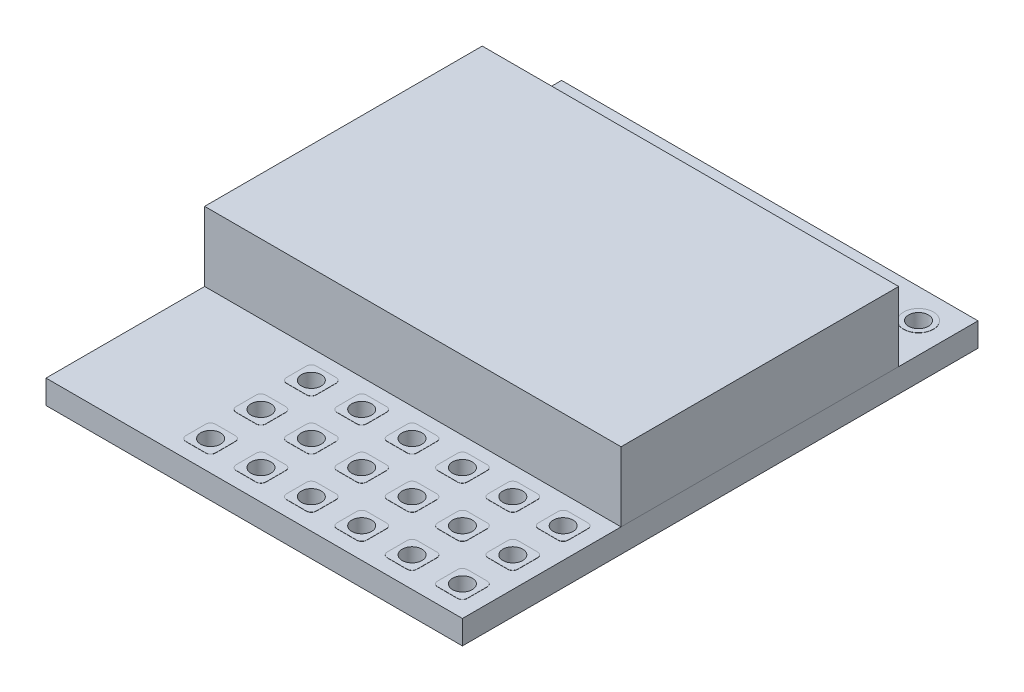
SolidWorks part; units mm, degrees
ref_plane "Front Plane" through (0, 0, 0) normal (0, 0, 1) x (1, 0, 0)
ref_plane "Top Plane" through (0, 0, 0) normal (0, 1, 0) x (1, 0, 0)
ref_plane "Right Plane" through (0, 0, 0) normal (1, 0, 0) x (0, 0, -1)
sketch "Sketch1" plane through (0, 0, 0) normal (0, 1, 0) x (1, 0, 0)
  line L1 (0, 0) -> (21, 0)
  line L2 (0, 0) -> (0, 26)
  line L3 (0, 26) -> (21, 26)
  line L4 (21, 0) -> (21, 26)
  dimension "D1" = 21
  dimension "D2" = 26
extrude "Boss-Extrude1" add sketch "Sketch1" along normal blind 1.2
sketch "Sketch3" plane through (0, 1.2, 0) normal (0, 1, 0) x (1, 0, 0)
  line L0 (21, 0) -> (21, 26) construction
  line L1 (21, 22) -> (0, 22)
  line L2 (21, 22) -> (21, 8)
  line L3 (21, 8) -> (0, 8)
  line L4 (0, 22) -> (0, 8)
  line L5 (0, 26) -> (0, 0) construction
  line L6 (21, 26) -> (0, 26) construction
  dimension "D1" = 14
  dimension "D2" = 4
extrude "Boss-Extrude2" add sketch "Sketch3" along normal blind 3.5 separate body
sketch "Sketch4" plane through (0, 1.2, 0) normal (0, 1, 0) x (1, 0, 0)
  line L0 (21, 0) -> (21, 26) construction
  line L1 (19, 2.25) -> (20, 2.25)
  line L2 (18.75, 2) -> (18.75, 1)
  line L3 (19, 0.75) -> (20, 0.75)
  line L4 (20.25, 2) -> (20.25, 1)
  line L5 (0, 0) -> (21, 0) construction
  line L6 (16.46, 2.25) -> (17.46, 2.25)
  line L7 (16.21, 2) -> (16.21, 1)
  line L8 (16.46, 0.75) -> (17.46, 0.75)
  line L9 (17.71, 2) -> (17.71, 1)
  line L10 (13.92, 2.25) -> (14.92, 2.25)
  line L11 (13.67, 2) -> (13.67, 1)
  line L12 (13.92, 0.75) -> (14.92, 0.75)
  line L13 (15.17, 2) -> (15.17, 1)
  line L14 (11.38, 2.25) -> (12.38, 2.25)
  line L15 (11.13, 2) -> (11.13, 1)
  line L16 (11.38, 0.75) -> (12.38, 0.75)
  line L17 (12.63, 2) -> (12.63, 1)
  line L18 (8.84, 2.25) -> (9.84, 2.25)
  line L19 (8.59, 2) -> (8.59, 1)
  line L20 (8.84, 0.75) -> (9.84, 0.75)
  line L21 (10.09, 2) -> (10.09, 1)
  line L22 (6.3, 2.25) -> (7.3, 2.25)
  line L23 (6.05, 2) -> (6.05, 1)
  line L24 (6.3, 0.75) -> (7.3, 0.75)
  line L25 (7.55, 2) -> (7.55, 1)
  line L26 (16.46, 4.79) -> (17.46, 4.79)
  line L27 (16.21, 4.54) -> (16.21, 3.54)
  line L28 (16.46, 3.29) -> (17.46, 3.29)
  line L29 (17.71, 4.54) -> (17.71, 3.54)
  line L30 (13.92, 4.79) -> (14.92, 4.79)
  line L31 (13.67, 4.54) -> (13.67, 3.54)
  line L32 (13.92, 3.29) -> (14.92, 3.29)
  line L33 (15.17, 4.54) -> (15.17, 3.54)
  line L34 (11.38, 4.79) -> (12.38, 4.79)
  line L35 (11.13, 4.54) -> (11.13, 3.54)
  line L36 (11.38, 3.29) -> (12.38, 3.29)
  line L37 (12.63, 4.54) -> (12.63, 3.54)
  line L38 (8.84, 4.79) -> (9.84, 4.79)
  line L39 (8.59, 4.54) -> (8.59, 3.54)
  line L40 (8.84, 3.29) -> (9.84, 3.29)
  line L41 (10.09, 4.54) -> (10.09, 3.54)
  line L42 (6.3, 4.79) -> (7.3, 4.79)
  line L43 (6.05, 4.54) -> (6.05, 3.54)
  line L44 (6.3, 3.29) -> (7.3, 3.29)
  line L45 (7.55, 4.54) -> (7.55, 3.54)
  line L46 (16.46, 7.33) -> (17.46, 7.33)
  line L47 (16.21, 7.08) -> (16.21, 6.08)
  line L48 (16.46, 5.83) -> (17.46, 5.83)
  line L49 (17.71, 7.08) -> (17.71, 6.08)
  line L50 (13.92, 7.33) -> (14.92, 7.33)
  line L51 (13.67, 7.08) -> (13.67, 6.08)
  line L52 (13.92, 5.83) -> (14.92, 5.83)
  line L53 (15.17, 7.08) -> (15.17, 6.08)
  line L54 (11.38, 7.33) -> (12.38, 7.33)
  line L55 (11.13, 7.08) -> (11.13, 6.08)
  line L56 (11.38, 5.83) -> (12.38, 5.83)
  line L57 (12.63, 7.08) -> (12.63, 6.08)
  line L58 (8.84, 7.33) -> (9.84, 7.33)
  line L59 (8.59, 7.08) -> (8.59, 6.08)
  line L60 (8.84, 5.83) -> (9.84, 5.83)
  line L61 (10.09, 7.08) -> (10.09, 6.08)
  line L62 (6.3, 7.33) -> (7.3, 7.33)
  line L63 (6.05, 7.08) -> (6.05, 6.08)
  line L64 (6.3, 5.83) -> (7.3, 5.83)
  line L65 (7.55, 7.08) -> (7.55, 6.08)
  line L66 (19, 4.79) -> (20, 4.79)
  line L67 (18.75, 4.54) -> (18.75, 3.54)
  line L68 (19, 3.29) -> (20, 3.29)
  line L69 (20.25, 4.54) -> (20.25, 3.54)
  line L70 (19, 7.33) -> (20, 7.33)
  line L71 (18.75, 7.08) -> (18.75, 6.08)
  line L72 (19, 5.83) -> (20, 5.83)
  line L73 (20.25, 7.08) -> (20.25, 6.08)
  circle A0 centre (19.5, 1.5) radius 0.5
  arc A1 (20, 0.75) -> (20.25, 1) centre (20, 1) ccw
  arc A2 (18.75, 1) -> (19, 0.75) centre (19, 1) ccw
  arc A3 (19, 2.25) -> (18.75, 2) centre (19, 2) ccw
  arc A4 (20, 2.25) -> (20.25, 2) centre (20, 2) cw
  circle A5 centre (16.96, 1.5) radius 0.5
  arc A6 (17.46, 0.75) -> (17.71, 1) centre (17.46, 1) ccw
  arc A7 (16.21, 1) -> (16.46, 0.75) centre (16.46, 1) ccw
  arc A8 (16.46, 2.25) -> (16.21, 2) centre (16.46, 2) ccw
  arc A9 (17.46, 2.25) -> (17.71, 2) centre (17.46, 2) cw
  circle A10 centre (14.42, 1.5) radius 0.5
  arc A11 (14.92, 0.75) -> (15.17, 1) centre (14.92, 1) ccw
  arc A12 (13.67, 1) -> (13.92, 0.75) centre (13.92, 1) ccw
  arc A13 (13.92, 2.25) -> (13.67, 2) centre (13.92, 2) ccw
  arc A14 (14.92, 2.25) -> (15.17, 2) centre (14.92, 2) cw
  circle A15 centre (11.88, 1.5) radius 0.5
  arc A16 (12.38, 0.75) -> (12.63, 1) centre (12.38, 1) ccw
  arc A17 (11.13, 1) -> (11.38, 0.75) centre (11.38, 1) ccw
  arc A18 (11.38, 2.25) -> (11.13, 2) centre (11.38, 2) ccw
  arc A19 (12.38, 2.25) -> (12.63, 2) centre (12.38, 2) cw
  circle A20 centre (9.34, 1.5) radius 0.5
  arc A21 (9.84, 0.75) -> (10.09, 1) centre (9.84, 1) ccw
  arc A22 (8.59, 1) -> (8.84, 0.75) centre (8.84, 1) ccw
  arc A23 (8.84, 2.25) -> (8.59, 2) centre (8.84, 2) ccw
  arc A24 (9.84, 2.25) -> (10.09, 2) centre (9.84, 2) cw
  circle A25 centre (6.8, 1.5) radius 0.5
  arc A26 (7.3, 0.75) -> (7.55, 1) centre (7.3, 1) ccw
  arc A27 (6.05, 1) -> (6.3, 0.75) centre (6.3, 1) ccw
  arc A28 (6.3, 2.25) -> (6.05, 2) centre (6.3, 2) ccw
  arc A29 (7.3, 2.25) -> (7.55, 2) centre (7.3, 2) cw
  circle A30 centre (16.96, 4.04) radius 0.5
  arc A31 (17.46, 3.29) -> (17.71, 3.54) centre (17.46, 3.54) ccw
  arc A32 (16.21, 3.54) -> (16.46, 3.29) centre (16.46, 3.54) ccw
  arc A33 (16.46, 4.79) -> (16.21, 4.54) centre (16.46, 4.54) ccw
  arc A34 (17.46, 4.79) -> (17.71, 4.54) centre (17.46, 4.54) cw
  circle A35 centre (14.42, 4.04) radius 0.5
  arc A36 (14.92, 3.29) -> (15.17, 3.54) centre (14.92, 3.54) ccw
  arc A37 (13.67, 3.54) -> (13.92, 3.29) centre (13.92, 3.54) ccw
  arc A38 (13.92, 4.79) -> (13.67, 4.54) centre (13.92, 4.54) ccw
  arc A39 (14.92, 4.79) -> (15.17, 4.54) centre (14.92, 4.54) cw
  circle A40 centre (11.88, 4.04) radius 0.5
  arc A41 (12.38, 3.29) -> (12.63, 3.54) centre (12.38, 3.54) ccw
  arc A42 (11.13, 3.54) -> (11.38, 3.29) centre (11.38, 3.54) ccw
  arc A43 (11.38, 4.79) -> (11.13, 4.54) centre (11.38, 4.54) ccw
  arc A44 (12.38, 4.79) -> (12.63, 4.54) centre (12.38, 4.54) cw
  circle A45 centre (9.34, 4.04) radius 0.5
  arc A46 (9.84, 3.29) -> (10.09, 3.54) centre (9.84, 3.54) ccw
  arc A47 (8.59, 3.54) -> (8.84, 3.29) centre (8.84, 3.54) ccw
  arc A48 (8.84, 4.79) -> (8.59, 4.54) centre (8.84, 4.54) ccw
  arc A49 (9.84, 4.79) -> (10.09, 4.54) centre (9.84, 4.54) cw
  circle A50 centre (6.8, 4.04) radius 0.5
  arc A51 (7.3, 3.29) -> (7.55, 3.54) centre (7.3, 3.54) ccw
  arc A52 (6.05, 3.54) -> (6.3, 3.29) centre (6.3, 3.54) ccw
  arc A53 (6.3, 4.79) -> (6.05, 4.54) centre (6.3, 4.54) ccw
  arc A54 (7.3, 4.79) -> (7.55, 4.54) centre (7.3, 4.54) cw
  circle A55 centre (16.96, 6.58) radius 0.5
  arc A56 (17.46, 5.83) -> (17.71, 6.08) centre (17.46, 6.08) ccw
  arc A57 (16.21, 6.08) -> (16.46, 5.83) centre (16.46, 6.08) ccw
  arc A58 (16.46, 7.33) -> (16.21, 7.08) centre (16.46, 7.08) ccw
  arc A59 (17.46, 7.33) -> (17.71, 7.08) centre (17.46, 7.08) cw
  circle A60 centre (14.42, 6.58) radius 0.5
  arc A61 (14.92, 5.83) -> (15.17, 6.08) centre (14.92, 6.08) ccw
  arc A62 (13.67, 6.08) -> (13.92, 5.83) centre (13.92, 6.08) ccw
  arc A63 (13.92, 7.33) -> (13.67, 7.08) centre (13.92, 7.08) ccw
  arc A64 (14.92, 7.33) -> (15.17, 7.08) centre (14.92, 7.08) cw
  circle A65 centre (11.88, 6.58) radius 0.5
  arc A66 (12.38, 5.83) -> (12.63, 6.08) centre (12.38, 6.08) ccw
  arc A67 (11.13, 6.08) -> (11.38, 5.83) centre (11.38, 6.08) ccw
  arc A68 (11.38, 7.33) -> (11.13, 7.08) centre (11.38, 7.08) ccw
  arc A69 (12.38, 7.33) -> (12.63, 7.08) centre (12.38, 7.08) cw
  circle A70 centre (9.34, 6.58) radius 0.5
  arc A71 (9.84, 5.83) -> (10.09, 6.08) centre (9.84, 6.08) ccw
  arc A72 (8.59, 6.08) -> (8.84, 5.83) centre (8.84, 6.08) ccw
  arc A73 (8.84, 7.33) -> (8.59, 7.08) centre (8.84, 7.08) ccw
  arc A74 (9.84, 7.33) -> (10.09, 7.08) centre (9.84, 7.08) cw
  circle A75 centre (6.8, 6.58) radius 0.5
  arc A76 (7.3, 5.83) -> (7.55, 6.08) centre (7.3, 6.08) ccw
  arc A77 (6.05, 6.08) -> (6.3, 5.83) centre (6.3, 6.08) ccw
  arc A78 (6.3, 7.33) -> (6.05, 7.08) centre (6.3, 7.08) ccw
  arc A79 (7.3, 7.33) -> (7.55, 7.08) centre (7.3, 7.08) cw
  circle A80 centre (19.5, 4.04) radius 0.5
  arc A81 (20, 3.29) -> (20.25, 3.54) centre (20, 3.54) ccw
  arc A82 (18.75, 3.54) -> (19, 3.29) centre (19, 3.54) ccw
  arc A83 (19, 4.79) -> (18.75, 4.54) centre (19, 4.54) ccw
  arc A84 (20, 4.79) -> (20.25, 4.54) centre (20, 4.54) cw
  circle A85 centre (19.5, 6.58) radius 0.5
  arc A86 (20, 5.83) -> (20.25, 6.08) centre (20, 6.08) ccw
  arc A87 (18.75, 6.08) -> (19, 5.83) centre (19, 6.08) ccw
  arc A88 (19, 7.33) -> (18.75, 7.08) centre (19, 7.08) ccw
  arc A89 (20, 7.33) -> (20.25, 7.08) centre (20, 7.08) cw
  dimension "D1" = 1
  dimension "D3" = 0.75
  dimension "D5" = 0.25
  dimension "D2" = 0.75
  dimension "D4" = 0.75
  dimension "D6" = 1.5
  dimension "D7" = 1.5
  dimension "D8" = 6
  dimension "D9" = 3
extrude "Boss-Extrude3" add sketch "Sketch4" along normal blind 0.01
sketch "Sketch6" plane through (0, 1.2, 0) normal (0, 1, 0) x (1, 0, 0)
  circle A0 centre (9.34, 6.58) radius 0.5 construction
  circle A1 centre (9.34, 4.04) radius 0.5 construction
  circle A2 centre (11.88, 4.04) radius 0.5 construction
  circle A3 centre (14.42, 4.04) radius 0.5 construction
  circle A4 centre (16.96, 4.04) radius 0.5 construction
  circle A5 centre (19.5, 4.04) radius 0.5 construction
  circle A6 centre (19.5, 6.58) radius 0.5 construction
  circle A7 centre (16.96, 6.58) radius 0.5 construction
  circle A8 centre (14.42, 6.58) radius 0.5 construction
  circle A9 centre (11.88, 6.58) radius 0.5 construction
  circle A10 centre (6.8, 6.58) radius 0.5 construction
  circle A11 centre (6.8, 4.04) radius 0.5 construction
  circle A12 centre (6.8, 1.5) radius 0.5 construction
  circle A13 centre (9.34, 1.5) radius 0.5 construction
  circle A14 centre (11.88, 1.5) radius 0.5 construction
  circle A15 centre (14.42, 1.5) radius 0.5 construction
  circle A16 centre (16.96, 1.5) radius 0.5 construction
  circle A17 centre (19.5, 1.5) radius 0.5 construction
  circle A18 centre (9.34, 6.58) radius 0.5
  circle A19 centre (9.34, 4.04) radius 0.5
  circle A20 centre (11.88, 4.04) radius 0.5
  circle A21 centre (14.42, 4.04) radius 0.5
  circle A22 centre (16.96, 4.04) radius 0.5
  circle A23 centre (19.5, 4.04) radius 0.5
  circle A24 centre (19.5, 6.58) radius 0.5
  circle A25 centre (16.96, 6.58) radius 0.5
  circle A26 centre (14.42, 6.58) radius 0.5
  circle A27 centre (11.88, 6.58) radius 0.5
  circle A28 centre (6.8, 6.58) radius 0.5
  circle A29 centre (6.8, 4.04) radius 0.5
  circle A30 centre (6.8, 1.5) radius 0.5
  circle A31 centre (9.34, 1.5) radius 0.5
  circle A32 centre (11.88, 1.5) radius 0.5
  circle A33 centre (14.42, 1.5) radius 0.5
  circle A34 centre (16.96, 1.5) radius 0.5
  circle A35 centre (19.5, 1.5) radius 0.5
extrude "Cut-Extrude1" cut sketch "Sketch6" against normal blind 4
sketch "Sketch7" plane through (0, 1.2, 0) normal (0, 1, 0) x (1, 0, 0)
  line L0 (21, 26) -> (0, 26) construction
  line L1 (21, 0) -> (21, 26) construction
  circle A0 centre (19.5, 24.5) radius 0.5
  circle A1 centre (19.5, 24.5) radius 0.75
  circle A2 centre (16.96, 24.5) radius 0.5
  circle A3 centre (16.96, 24.5) radius 0.75
  circle A4 centre (14.42, 24.5) radius 0.5
  circle A5 centre (14.42, 24.5) radius 0.75
  circle A6 centre (11.88, 24.5) radius 0.5
  circle A7 centre (11.88, 24.5) radius 0.75
  circle A8 centre (9.34, 24.5) radius 0.5
  circle A9 centre (9.34, 24.5) radius 0.75
  circle A10 centre (6.8, 24.5) radius 0.5
  circle A11 centre (6.8, 24.5) radius 0.75
  circle A12 centre (4.26, 24.5) radius 0.5
  circle A13 centre (4.26, 24.5) radius 0.75
  circle A14 centre (1.72, 24.5) radius 0.5
  circle A15 centre (1.72, 24.5) radius 0.75
  dimension "D1" = 1
  dimension "D2" = 1.5
  dimension "D3" = 1.5
  dimension "D5" = 1.5
  dimension "D4" = 8
extrude "Boss-Extrude4" add sketch "Sketch7" along normal blind 0.01
sketch "Sketch8" plane through (0, 1.2, 0) normal (0, 1, 0) x (1, 0, 0)
  circle A1 centre (19.5, 24.5) radius 0.5
  circle A2 centre (19.5, 24.5) radius 0.5
  circle A3 centre (16.96, 24.5) radius 0.5
  circle A4 centre (16.96, 24.5) radius 0.5
  circle A5 centre (14.42, 24.5) radius 0.5
  circle A6 centre (14.42, 24.5) radius 0.5
  circle A7 centre (11.88, 24.5) radius 0.5
  circle A8 centre (11.88, 24.5) radius 0.5
  circle A9 centre (9.34, 24.5) radius 0.5
  circle A10 centre (9.34, 24.5) radius 0.5
  circle A11 centre (6.8, 24.5) radius 0.5
  circle A12 centre (6.8, 24.5) radius 0.5
  circle A13 centre (4.26, 24.5) radius 0.5
  circle A14 centre (4.26, 24.5) radius 0.5
  circle A15 centre (1.72, 24.5) radius 0.5
  circle A16 centre (1.72, 24.5) radius 0.5
  dimension "D1" = 0
  dimension "D2" = 0
  dimension "D3" = 0
  dimension "D4" = 0
  dimension "D5" = 0
  dimension "D6" = 0
  dimension "D7" = 0
  dimension "D8" = 0
extrude "Cut-Extrude2" cut sketch "Sketch8" against normal blind 4
